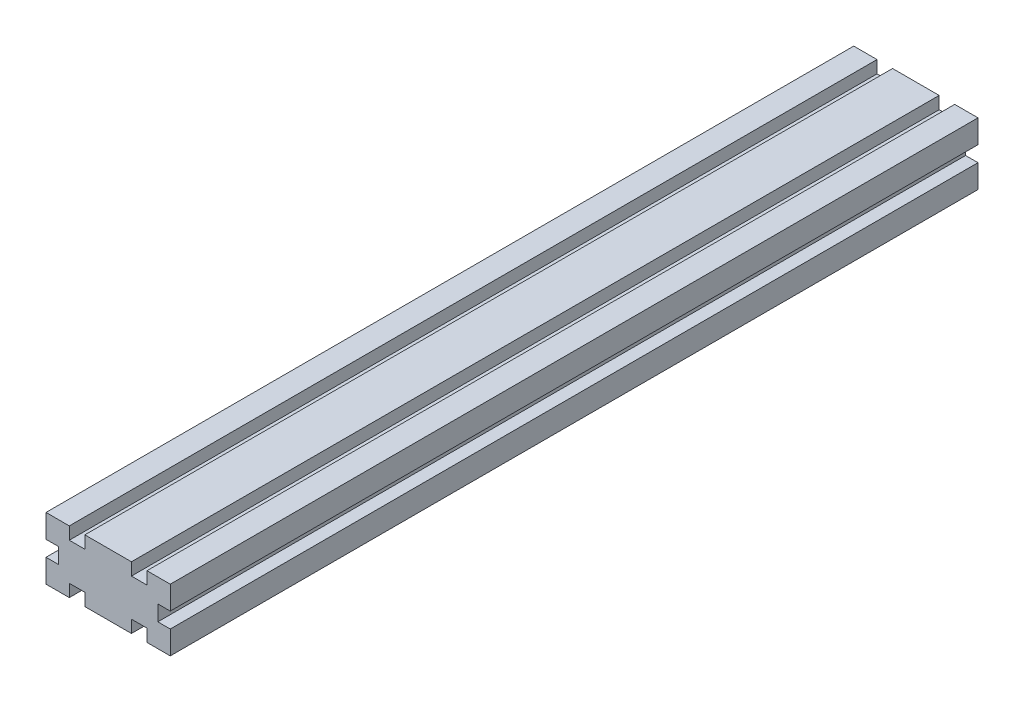
SolidWorks part; units mm, degrees
ref_plane "Plan de face" through (0, 0, 0) normal (0, 0, 1) x (1, 0, 0)
ref_plane "Plan de dessus" through (0, 0, 0) normal (0, 1, 0) x (1, 0, 0)
ref_plane "Plan de droite" through (0, 0, 0) normal (1, 0, 0) x (0, 0, -1)
sketch "Esquisse1" plane through (0, 0, 0) normal (0, 0, 1) x (1, 0, 0)
  line L0 (20, 20) -> (20, 0)
  line L1 (0, 0) -> (40, 0)
  line L2 (0, 0) -> (0, 20)
  line L3 (0, 20) -> (40, 20)
  line L4 (40, 0) -> (40, 20)
  line L5 (20, 0) -> (40, 20)
  line L6 (40, 0) -> (20, 20)
  line L7 (0, 0) -> (20, 20)
  line L8 (20, 0) -> (0, 20)
  line L10 (4, 4) -> (16, 4)
  line L11 (4, 4) -> (4, 16)
  line L12 (4, 16) -> (16, 16)
  line L13 (16, 4) -> (16, 16)
  line L14 (4, 4) -> (16, 16) construction
  line L15 (4, 16) -> (16, 4) construction
  line L16 (24, 4) -> (36, 4)
  line L17 (24, 4) -> (24, 16)
  line L18 (24, 16) -> (36, 16)
  line L19 (36, 4) -> (36, 16)
  line L20 (24, 4) -> (36, 16) construction
  line L21 (24, 16) -> (36, 4) construction
  line L22 (12.5, 0) -> (7.5, 0)
  line L23 (12.5, 0) -> (12.5, 20)
  line L24 (12.5, 20) -> (7.5, 20)
  line L25 (7.5, 0) -> (7.5, 20)
  line L26 (12.5, 0) -> (7.5, 20) construction
  line L27 (12.5, 20) -> (7.5, 0) construction
  line L28 (32.5, 0) -> (27.5, 0)
  line L29 (32.5, 0) -> (32.5, 20)
  line L30 (32.5, 20) -> (27.5, 20)
  line L31 (27.5, 0) -> (27.5, 20)
  line L32 (32.5, 0) -> (27.5, 20) construction
  line L33 (32.5, 20) -> (27.5, 0) construction
  line L34 (0, 7.5) -> (40, 7.5)
  line L35 (0, 7.5) -> (0, 12.5)
  line L36 (0, 12.5) -> (40, 12.5)
  line L37 (40, 7.5) -> (40, 12.5)
  line L38 (0, 7.5) -> (40, 12.5) construction
  line L39 (0, 12.5) -> (40, 7.5) construction
  point P7 (10, 10)
  point P12 (30, 10)
  point P17 (10, 10)
  point P22 (30, 10)
  point P27 (20, 10)
  dimension "D1" = 20
  dimension "D2" = 40
  dimension "D3" = 12
  dimension "D5" = 5
  dimension "D6" = 5
  dimension "D7" = 5
extrude "Boss.-Extru.1" add sketch "Esquisse1" along normal blind 260 contours L12 L25 L3 L8 | L2 L36 L11 L8 | L34 L2 L7 L11 | L1 L25 L10 L7 | L34 L11 L7 | L10 L25 L7 | L11 L36 L8 | L8 L25 L12 | L36 L11 L34 L25 | L25 L7 L8 | L36 L8 L7 | L8 L23 L7 | L7 L34 L8 | L23 L10 L8 | L34 L8 L13 | L34 L13 L8 L0 | L25 L36 L23 L12 | L36 L23 L34 L13 | L23 L7 L12 | L23 L12 L7 L3 | L7 L36 L13 | L13 L36 L0 L7 | L23 L1 L8 L10 | L34 L25 L10 L23 | L36 L13 L34 L0 | L36 L0 L34 L17 | L0 L36 L17 L6 | L18 L31 L3 L6 | L17 L36 L6 | L6 L31 L18 | L36 L17 L34 L31 | L34 L17 L5 | L34 L0 L5 L17 | L1 L31 L16 L5 | L16 L31 L5 | L34 L31 L16 L29 | L29 L16 L6 | L34 L6 L19 | L34 L19 L6 L4 | L29 L1 L6 L16 | L36 L29 L34 L19 | L6 L29 L5 | L5 L34 L6 | L31 L5 L6 | L36 L6 L5 | L5 L36 L19 | L29 L5 L18 | L29 L18 L5 L3 | L19 L36 L4 L5 | L31 L36 L29 L18
